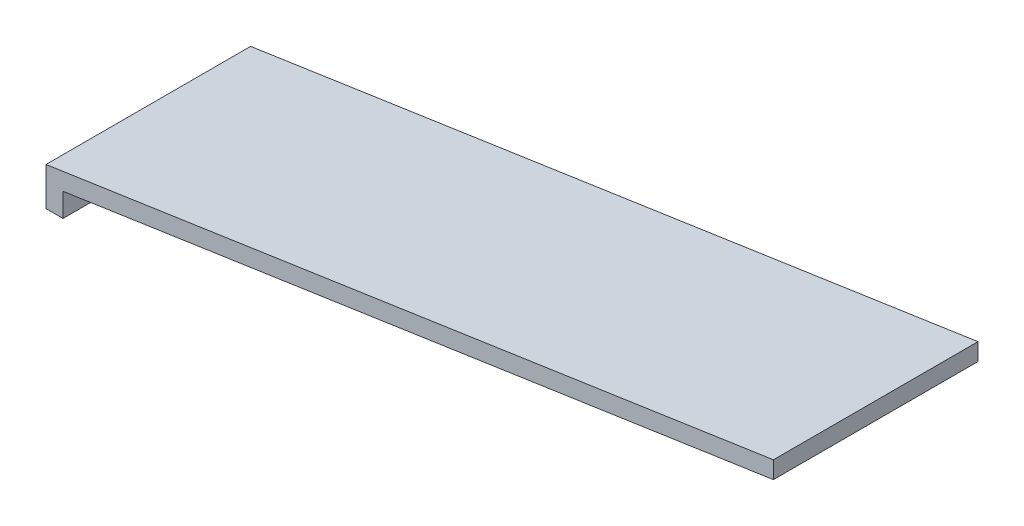
SolidWorks part; units mm, degrees
ref_plane "Front Plane" through (0, 0, 0) normal (0, 0, 1) x (1, 0, 0)
ref_plane "Top Plane" through (0, 0, 0) normal (0, 1, 0) x (1, 0, 0)
ref_plane "Right Plane" through (0, 0, 0) normal (1, 0, 0) x (0, 0, -1)
ref_plane "Plane1" through (0, 0, 2.15) normal (0, 0, 1) x (1, 0, 0)
sketch "Sketch1" plane through (0, 0, 2.15) normal (0, 0, 1) x (1, 0, 0)
  line L0 (-0.8, 0.3929) -> (-0.8, -0.2801)
  line L1 (-0.8, -0.2801) -> (-0.5, -0.2801)
  line L3 (12, 2.2929) -> (-0.8, 0.3929)
  line L4 (12, -0.2801) -> (12, 16.2687) construction
  line L5 (12, -0.2801) -> (12, 2.2929) construction
  line L7 (-0.5, -0.2801) -> (-0.5, 0.1342)
  line L8 (12, 1.9897) -> (-0.5, 0.1342)
  line L9 (12, 2.2929) -> (12, 1.9897)
  line L10 (12.044, 1.9962) -> (-0.756, 0.0962) construction
  dimension "D1" = 0.3
  dimension "D3" = 0.3
extrude "Boss-Extrude1" add sketch "Sketch1" against normal blind 3.6
